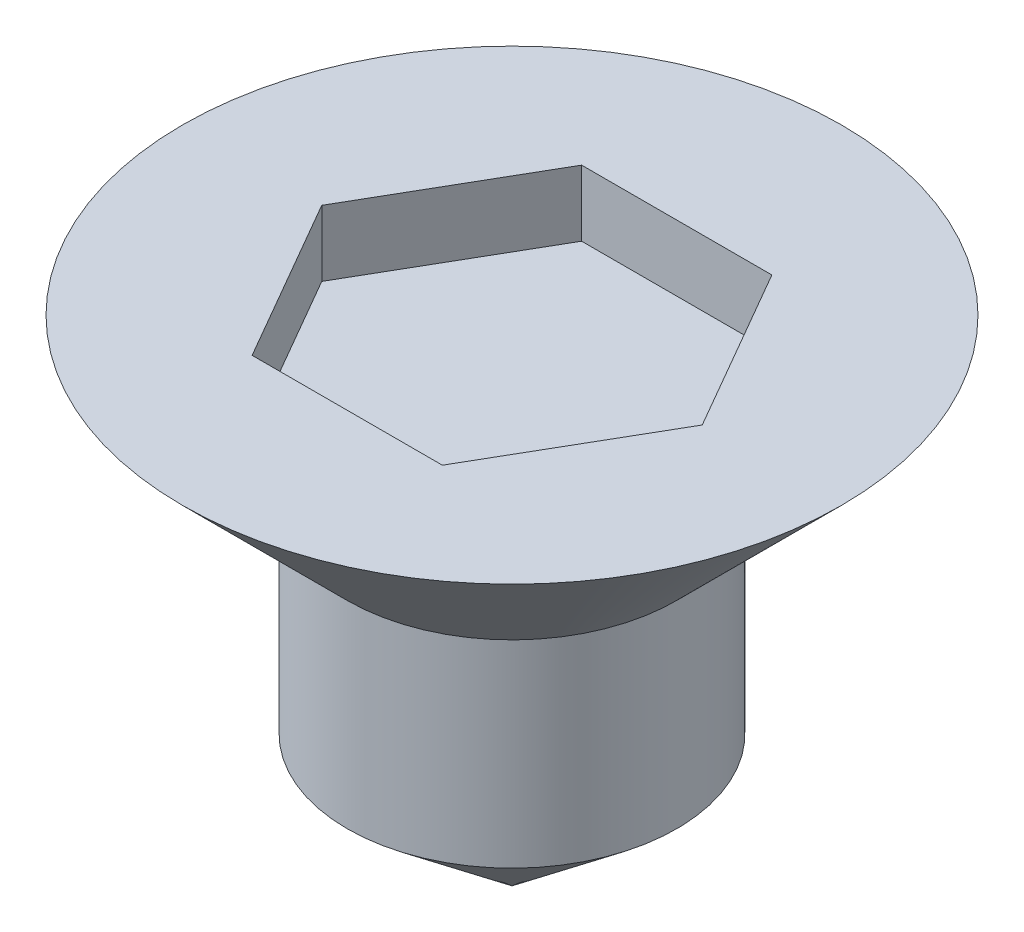
SolidWorks part; units mm, degrees
ref_plane "Alzado" through (0, 0, 0) normal (0, 0, 1) x (1, 0, 0)
ref_plane "Planta" through (0, 0, 0) normal (0, 1, 0) x (1, 0, 0)
ref_plane "Vista lateral" through (0, 0, 0) normal (1, 0, 0) x (0, 0, -1)
sketch "Croquis1" plane through (0, 0, 0) normal (0, 1, 0) x (1, 0, 0)
  circle A0 centre (0, 0) radius 1.25
  dimension "D1" = 2.5
extrude "Saliente-Extruir1" add sketch "Croquis1" along normal blind 1.5
sketch "Croquis2" plane through (0, 0, 0) normal (1, 0, 0) x (0, 0, -1)
  line L0 (-1.25, 1.5) -> (-2.5, 2.75)
  line L1 (-2.5, 2.75) -> (2.5, 2.75)
  line L2 (2.5, 2.75) -> (1.25, 1.5)
  line L3 (1.25, 1.5) -> (-1.25, 1.5)
  line L4 (0, 2.75) -> (0, 1.5) construction
  point P6 (0, 2.75)
  point P7 (0, 1.5)
  dimension "D1" = 5
  dimension "D2" = 90
revolve "Revolución1" add sketch "Croquis2" angle 360 about L4
sketch "Croquis3" plane through (0, 2.75, 0) normal (0, 1, 0) x (1, 0, 0)
  line L1 (1.4434, 0) -> (0.7217, 1.25)
  line L2 (0.7217, 1.25) -> (-0.7217, 1.25)
  line L3 (-0.7217, 1.25) -> (-1.4434, 0)
  line L4 (-1.4434, 0) -> (-0.7217, -1.25)
  line L5 (-0.7217, -1.25) -> (0.7217, -1.25)
  line L6 (0.7217, -1.25) -> (1.4434, 0)
  circle A0 centre (0, 0) radius 1.25 construction
  dimension "D1" = 2.5
extrude "Cortar-Extruir1" cut sketch "Croquis3" against normal blind 0.5
sketch "Croquis4" plane through (0, 0, 0) normal (0, 0, 1) x (1, 0, 0)
  line L0 (-1.25, 0) -> (0, -1)
  line L1 (0, -1) -> (1.25, 0)
  line L2 (1.25, 0) -> (-1.25, 0)
  line L3 (0, 0) -> (0, -1) construction
  dimension "D1" = 1
revolve "Revolución2" add sketch "Croquis4" angle 360 about L3
